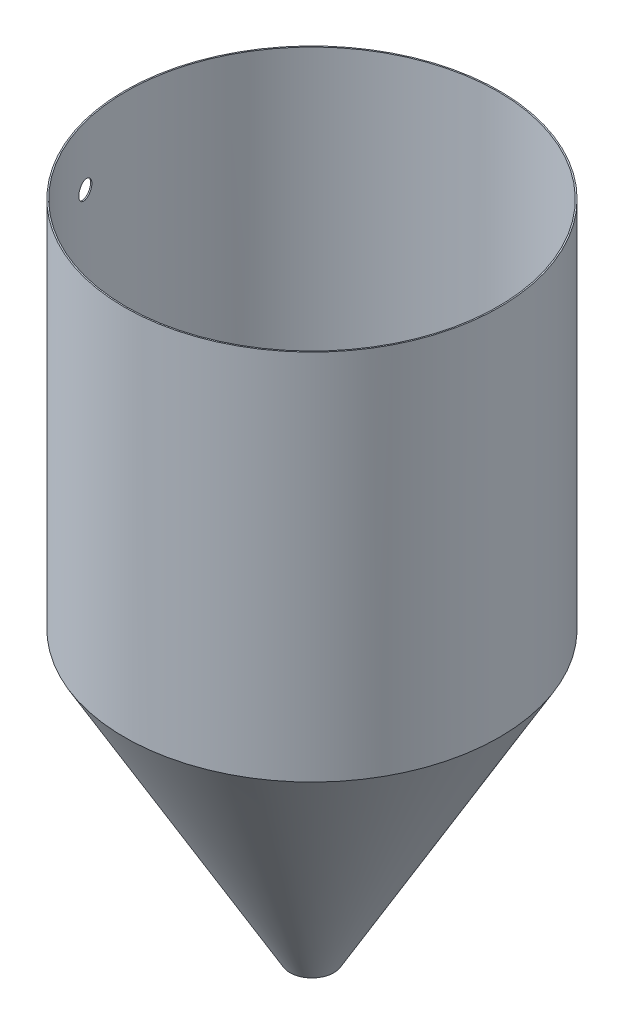
SolidWorks part; units mm, degrees
material "AISI 304"
ref_plane "Front Plane" through (0, 0, 0) normal (0, 0, 1) x (1, 0, 0)
ref_plane "Top Plane" through (0, 0, 0) normal (0, 1, 0) x (1, 0, 0)
ref_plane "Right Plane" through (0, 0, 0) normal (1, 0, 0) x (0, 0, -1)
sketch "Sketch7" plane through (0, 0, 0) normal (0, 1, 0) x (1, 0, 0)
  circle A0 centre (0, 0) radius 228.6
  circle A1 centre (0, 0) radius 230.1875
  dimension "D1" = 457.2
  dimension "D2" = 1.5875
extrude "Boss-Extrude1" add sketch "Sketch7" along normal blind 457.2
sketch "Sketch8" plane through (0, 0, 0) normal (0, 0, 1) x (1, 0, 0)
  line L0 (0, 0) -> (0, -395.9468) construction
  line L1 (0, -395.9468) -> (228.6, 0) construction
  line L2 (-228.6, 0) -> (228.6, 0) construction
  line L3 (-230.1875, 0) -> (230.1875, 0) construction
  line L4 (228.6, 0) -> (230.1875, 0)
  line L5 (228.6, 0) -> (25.4, -351.9527)
  line L6 (25.4, -351.9527) -> (26.9875, -351.9527)
  line L7 (26.9875, -351.9527) -> (230.1875, 0)
  dimension "D1" = 457.2
  dimension "D2" = 457.2
  dimension "D3" = 406.4
revolve "Revolve1" add sketch "Sketch8" angle 360 about L0
sketch "Sketch9" plane through (0, 0, 0) normal (1, 0, 0) x (0, 0, -1)
  circle A0 centre (-57.15, 384.9808) radius 10.795
  dimension "D1" = 21.59
extrude "Cut-Extrude1" cut sketch "Sketch9" against normal blind 304.8
